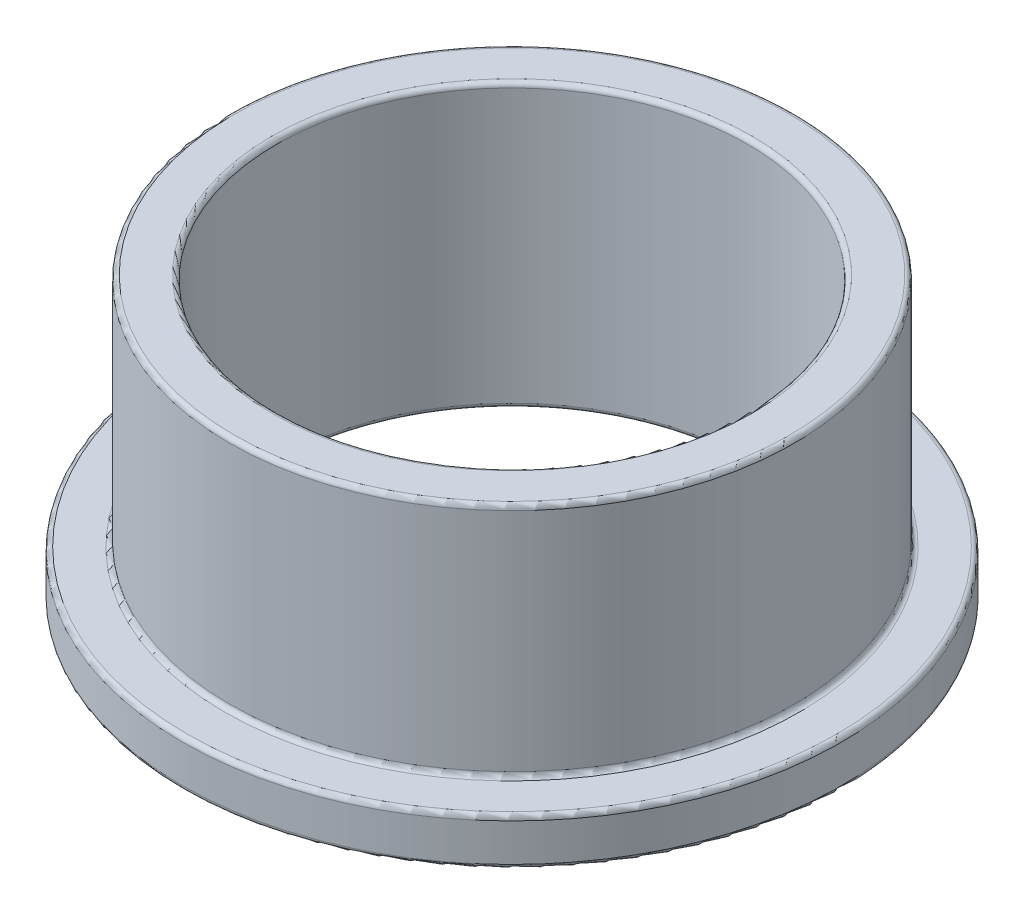
SolidWorks part; units mm, degrees
material "Commercial Bronze, UNS C22000 (90-10 Bronze)"
ref_plane "Front" through (0, 0, 0) normal (0, 0, 1) x (1, 0, 0)
ref_plane "Top" through (0, 0, 0) normal (0, 1, 0) x (1, 0, 0)
ref_plane "Right" through (0, 0, 0) normal (1, 0, 0) x (0, 0, -1)
sketch "Sketch1" plane through (0, 0, 0) normal (0, 1, 0) x (1, 0, 0)
  circle A0 centre (0, 0) radius 5
  circle A1 centre (0, 0) radius 6
  circle A2 centre (0, 0) radius 7
  dimension "ID" = 10
  dimension "OD" = 12
  dimension "FlangeOD" = 14
sketch "Sketch2" plane through (0, 0, 0) normal (1, 0, 0) x (0, 0, -1)
  line L0 (7, 0) -> (7, 1) construction
  line L1 (-6, 0) -> (-6, 6) construction
  line L8 (0, 0) -> (0, 6) construction
  point P5 (-7, 0)
  dimension "Flange Thickness" = 1
  dimension "Length" = 6
sketch "Sketch3" plane through (0, 0, 0) normal (0, 1, 0) x (1, 0, 0)
  circle A0 centre (0, 0) radius 5 construction
  circle A1 centre (0, 0) radius 6 construction
  circle A2 centre (0, 0) radius 5
  circle A3 centre (0, 0) radius 6
extrude "Boss-Extrude1" add sketch "Sketch3" along normal up to vertex (6 mm away) up to point (0, 6, 6)
sketch "Sketch4" plane through (0, 0, 0) normal (0, 1, 0) x (1, 0, 0)
  circle A0 centre (0, 0) radius 7 construction
  circle A1 centre (0, 0) radius 6 construction
  circle A2 centre (0, 0) radius 7
  circle A3 centre (0, 0) radius 6
extrude "Boss-Extrude2" add sketch "Sketch4" along normal up to vertex (1 mm away) up to point (0, 1, -7)
fillet "Fillet1" radius 0.1 6 edges at (0, 0, 5) (0, 0, 7) (0, 1, 6) (0, 1, 7) (0, 6, 5) (0, 6, 6)
equation "\"D1@Fillet1\"=(\"OD@Sketch1\"-\"ID@Sketch1\")*.05"
